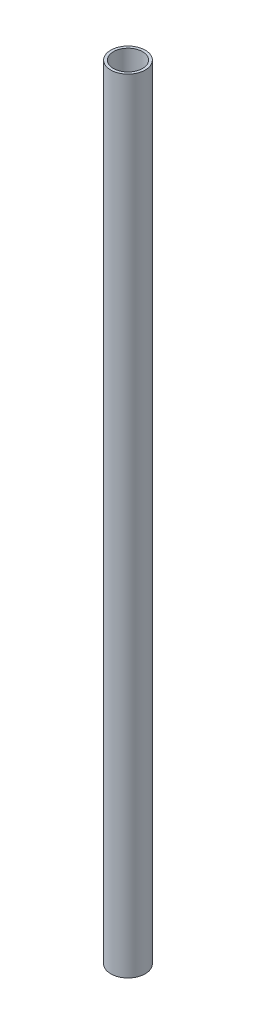
SolidWorks part; units mm, degrees
material "普通碳钢"
ref_plane "前视基准面" through (0, 0, 0) normal (0, 0, 1) x (1, 0, 0)
ref_plane "上视基准面" through (0, 0, 0) normal (0, 1, 0) x (1, 0, 0)
ref_plane "右视基准面" through (0, 0, 0) normal (1, 0, 0) x (0, 0, -1)
sketch "草图1" plane through (0, 0, 0) normal (0, 1, 0) x (1, 0, 0)
  circle A0 centre (0, 0) radius 11
  circle A1 centre (0, 0) radius 13
  dimension "D1" = 22
  dimension "D2" = 26
extrude "凸台-拉伸1" add sketch "草图1" along normal blind 590
sketch "草图2" plane through (0, 0, 0) normal (1, 0, 0) x (0, 0, -1)
  line L0 (0, 0) -> (0, 590) construction
  line L1 (11, 590) -> (-11, 590) construction
  circle A0 centre (0, 22.5) radius 2.5
  circle A1 centre (0, 571.5) radius 2.5
  dimension "D1" = 5
  dimension "D2" = 5
  dimension "D3" = 22.5
  dimension "D4" = 18.5
extrude "切除-拉伸1" cut sketch "草图2" against normal through all
